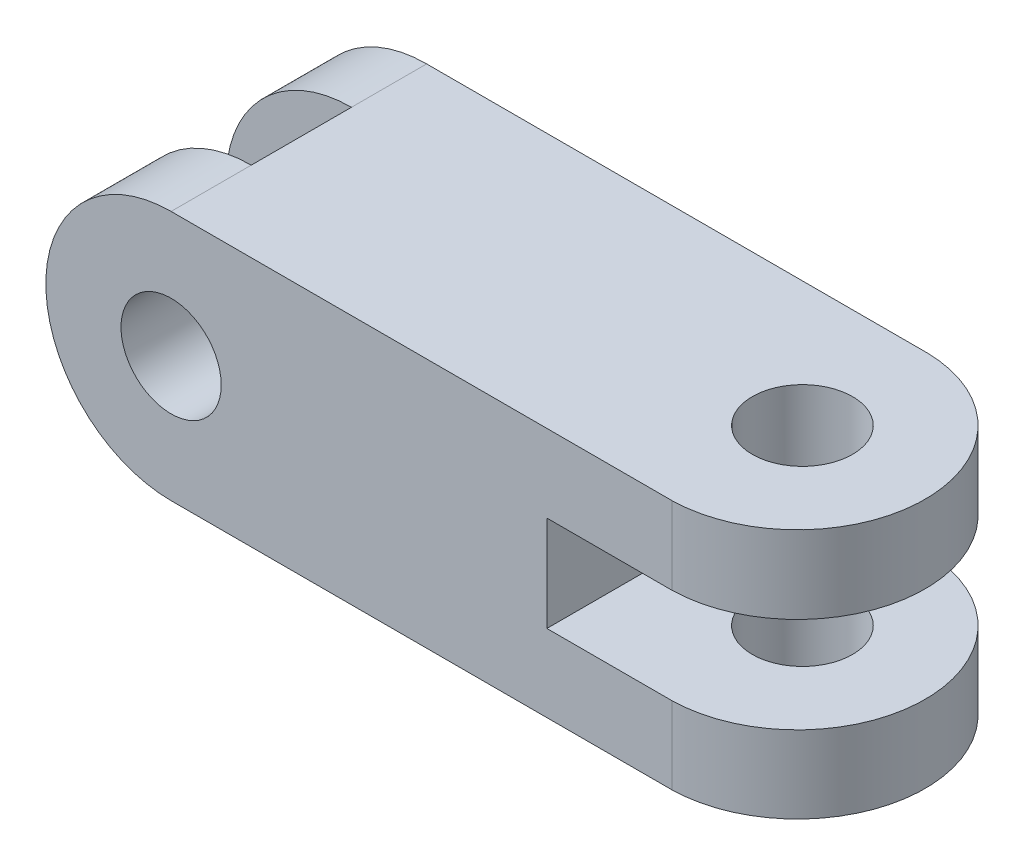
SolidWorks part; units mm, degrees
ref_plane "Front Plane" through (0, 0, 0) normal (0, 0, 1) x (1, 0, 0)
ref_plane "Top Plane" through (0, 0, 0) normal (0, 1, 0) x (1, 0, 0)
ref_plane "Right Plane" through (0, 0, 0) normal (1, 0, 0) x (0, 0, -1)
sketch "Sketch1" plane through (0, 0, 0) normal (0, 0, 1) x (1, 0, 0)
  line L0 (90.4673, -12.2906) -> (40.4673, -12.2906)
  line L1 (-34.5327, 3.2094) -> (90.4673, 3.2094)
  line L3 (-34.5327, -46.7906) -> (90.4673, -46.7906)
  line L4 (90.4673, 3.2094) -> (90.4673, -12.2906)
  line L5 (40.4673, -12.2906) -> (40.4673, -31.3736)
  line L6 (40.4673, -31.3736) -> (90.4673, -31.3736)
  line L7 (90.4673, -31.3736) -> (90.4673, -46.7906)
  arc A0 (-34.5327, 3.2094) -> (-34.5327, -46.7906) centre (-34.5327, -21.7906) ccw
  circle A1 centre (-34.5327, -21.7906) radius 10
extrude "Boss-Extrude1" add sketch "Sketch1" along normal blind 50 and the other way blind 1
sketch "Sketch2" plane through (0, 3.2094, 0) normal (0, 1, 0) x (1, 0, 0)
  line L7 (90.4673, 1) -> (-34.5327, 1) construction
  line L8 (90.4673, -50) -> (-34.5327, -50) construction
  line L9 (-59.5327, 1) -> (-59.5327, -50) construction
  line L10 (-59.5327, -14) -> (-34.5327, -14)
  line L11 (-59.5327, -14) -> (-59.5327, -34)
  line L12 (-59.5327, -34) -> (-34.5327, -34)
  line L13 (-34.5327, -14) -> (-34.5327, -34)
  line L14 (-34.5327, 1) -> (-34.5327, -50) construction
  circle A0 centre (65.4673, -24) radius 10
  arc A1 (65.4673, 1) -> (65.4673, -50) centre (64.9623, -24.5) cw
  line M2 (-34.5327, 1) -> (-34.5327, -50)
  line M3 (-34.5327, -50) -> (90.4673, -50)
  line M4 (90.4673, -50) -> (90.4673, 1)
  line M5 (90.4673, 1) -> (-34.5327, 1)
extrude "Cut-Extrude3" cut sketch "Sketch2" against normal blind 50 contours L11 L12 L10 M2 | A0 | A1 M4 M3 | A1 M5 M4
